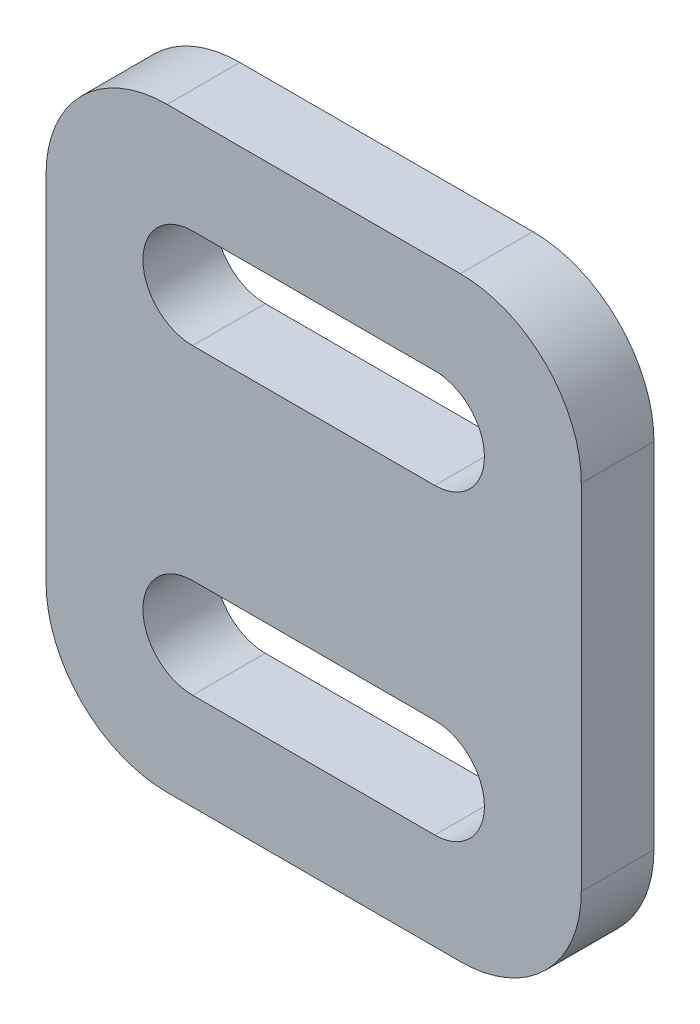
SolidWorks part; units mm, degrees
material "Gerais  - 6061-T6"
ref_plane "Plano frontal" through (0, 0, 0) normal (0, 0, 1) x (1, 0, 0)
ref_plane "Plano superior" through (0, 0, 0) normal (0, 1, 0) x (1, 0, 0)
ref_plane "Plano direito" through (0, 0, 0) normal (1, 0, 0) x (0, 0, -1)
sketch "Esboço1" plane through (0, 0, 0) normal (0, 0, 1) x (1, 0, 0)
  line L0 (31.0719, 33.6305) -> (31.0719, 0) construction
  line L1 (16.0719, 26.4418) -> (16.0719, 19.9575) construction
  line L2 (20, 33.6305) -> (31.0719, 33.6305)
  line L3 (20, 40.9805) -> (8.8219, 19.9575) construction
  line L4 (31.0719, 0) -> (14.25, 0) construction
  line L5 (31.0719, 26.5) -> (16.0719, 26.5) construction
  line L6 (22.1219, 26.5) -> (22.1219, 14) construction
  line L9 (38.1719, 7.95) -> (16.0719, 7.95)
  line L10 (38.1719, 7.95) -> (38.1719, 32.55)
  line L11 (38.1719, 32.55) -> (16.0719, 32.55)
  line L12 (16.0719, 7.95) -> (16.0719, 32.55)
  line L13 (38.1719, 7.95) -> (16.0719, 32.55) construction
  line L14 (38.1719, 32.55) -> (16.0719, 7.95) construction
  line L15 (22.1219, 26.5) -> (32.1219, 26.5) construction
  line L16 (22.1219, 28.55) -> (32.1219, 28.55)
  line L17 (22.1219, 24.45) -> (32.1219, 24.45)
  line L18 (22.1219, 14) -> (32.1219, 14) construction
  line L19 (22.1219, 16.05) -> (32.1219, 16.05)
  line L20 (22.1219, 11.95) -> (32.1219, 11.95)
  circle A0 centre (0, 0) radius 7.25 construction
  circle A1 centre (0, 0) radius 14.25 construction
  circle A2 centre (20, 40.9805) radius 23.81 construction
  arc A3 (20, 33.6305) -> (20, 48.3305) centre (20, 40.9805) cw construction
  arc A4 (20, 48.3305) -> (20, 56.0405) centre (20, 52.1855) ccw construction
  circle A5 centre (8.8219, 19.9575) radius 7.25 construction
  arc A6 (16.0719, 19.9575) -> (5.6354, 13.0883) centre (8.5931, 19.9575) cw construction
  arc A7 (20, 56.0405) -> (16.0719, 26.4418) centre (20, 40.9805) ccw construction
  arc A10 (22.1219, 28.55) -> (22.1219, 24.45) centre (22.1219, 26.5) ccw
  arc A11 (32.1219, 24.45) -> (32.1219, 28.55) centre (32.1219, 26.5) ccw
  arc A12 (22.1219, 16.05) -> (22.1219, 11.95) centre (22.1219, 14) ccw
  arc A13 (32.1219, 11.95) -> (32.1219, 16.05) centre (32.1219, 14) ccw
  point P4 (12.2256, 26.3589)
  point P5 (-7.25, 0)
  point P6 (-14.25, 0)
  point P8 (12.9298, 27.6833)
  point P25 (22.1219, 20.25)
  point P26 (27.1219, 20.25)
  point P35 (27.1219, 26.5)
  point P39 (22.1219, 11.95)
  point P42 (27.1219, 14)
  point P48 (34.1719, 26.5)
  point P51 (27.1219, 32.55)
  dimension "D1" = 7.35
  dimension "D2" = 14.5
  dimension "D6" = 47.62
  dimension "D10" = 2.05
  dimension "D3" = 7
  dimension "D4" = 1.5
  dimension "D5" = 45.6004
  dimension "D7" = 28
  dimension "D8" = 15
  dimension "D9" = 20
  dimension "D11" = 12.5
  dimension "D12" = 14
  dimension "D13" = 4
  dimension "D14" = 4
  dimension "D15" = 10
extrude "Ressalto-extrusão1" add sketch "Esboço1" along normal blind 3 contours A4 A7 L1 A6 A1 L0 L2 A3 | A1 A0 | L12 L9 L10 L11 A13 L20 A12 L19 A11 L17 A10 L16
fillet "Filete1" radius 5 4 edges at (16.0719, 32.55, 1.5) (16.0719, 7.95, 1.5) (38.1719, 7.95, 1.5) (38.1719, 32.55, 1.5)
